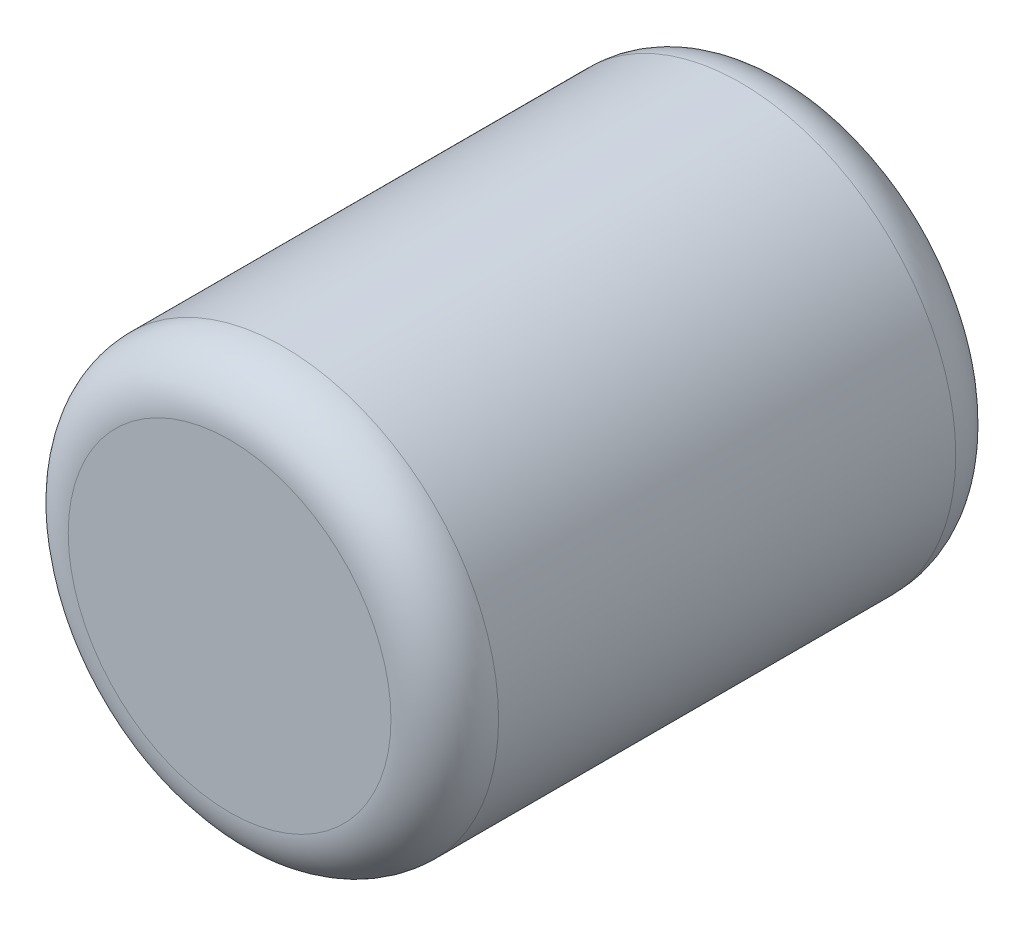
SolidWorks part; units mm, degrees
ref_plane "Front Plane" through (0, 0, 0) normal (0, 0, 1) x (1, 0, 0)
ref_plane "Top Plane" through (0, 0, 0) normal (0, 1, 0) x (1, 0, 0)
ref_plane "Right Plane" through (0, 0, 0) normal (1, 0, 0) x (0, 0, -1)
sketch "Sketch1" plane through (0, 0, 0) normal (0, 0, 1) x (1, 0, 0)
  circle A0 centre (0, 0) radius 50.8
extrude "Boss-Extrude1" add sketch "Sketch1" along normal blind 133.35
fillet "Fillet1" radius 12.7 2 edges at (50.8, 0, 0) (50.8, 0, 133.35)
